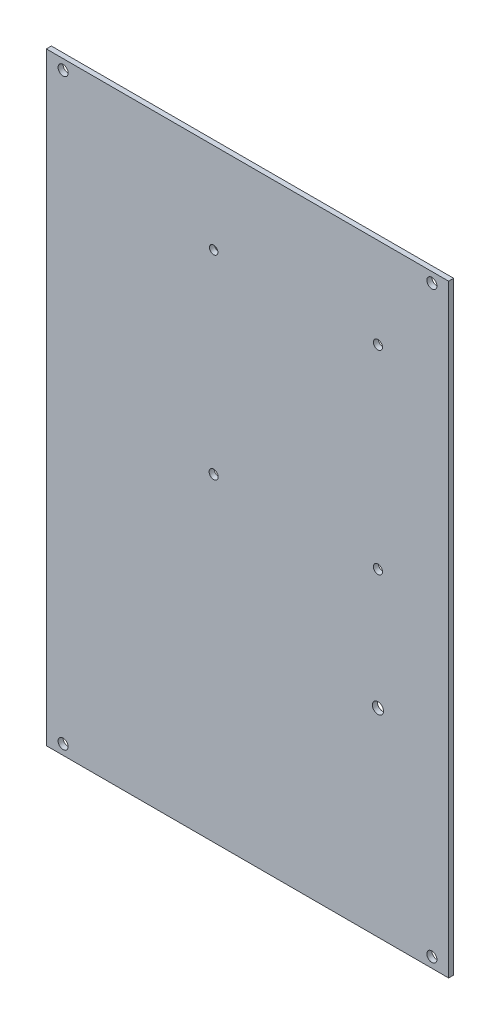
SolidWorks part; units mm, degrees
material "1060 合金"
ref_plane "前视基准面" through (0, 0, 0) normal (0, 0, 1) x (1, 0, 0)
ref_plane "上视基准面" through (0, 0, 0) normal (0, 1, 0) x (1, 0, 0)
ref_plane "右视基准面" through (0, 0, 0) normal (1, 0, 0) x (0, 0, -1)
sketch "草图1" plane through (0, 0, 0) normal (0, 0, 1) x (1, 0, 0)
  line L16 (311.4527, 900) -> (311.4527, -900)
  line L17 (311.4527, 900) -> (1511.4527, 900)
  line L18 (1511.4527, 900) -> (1511.4527, -900)
  line L19 (311.4527, -900) -> (1511.4527, -900)
  circle A20 centre (361.4527, 870) radius 15
  circle A25 centre (810.563, 50.4942) radius 13.5
  circle A26 centre (1300.563, 50.4942) radius 13.5
  circle A27 centre (1300.563, 630.408) radius 13.5
  circle A28 centre (810.563, 630.408) radius 12.5
  circle A29 centre (1461.4527, 870) radius 15
  circle A30 centre (361.4527, -870) radius 15
  circle A31 centre (1461.4527, -870) radius 15
  circle A32 centre (1300.563, -308.2038) radius 16.51
  point P4 (1137.1335, -307.5908)
  dimension "D4" = 210.8898
  dimension "D5" = 591.7962
  dimension "D73" = 30
  dimension "D99" = 490
  dimension "D98" = 579.9138
  dimension "D100" = 490
  dimension "D102" = 27
  dimension "D104" = 25
  dimension "D19" = 1200
  dimension "D23" = 1800
  dimension "D36" = 50
  dimension "D37" = 30
  dimension "D65" = 579.9138
  dimension "D66" = 269.592
  dimension "D70" = 50
extrude "凸台-拉伸1" add sketch "草图1" along normal blind 3
scale "缩放比例1" bodies to scale 101 104 102 103 108 scale about centroid uniform scaling no x scale factor 0.1 y scale factor 0.1 z scale factor 0.5
